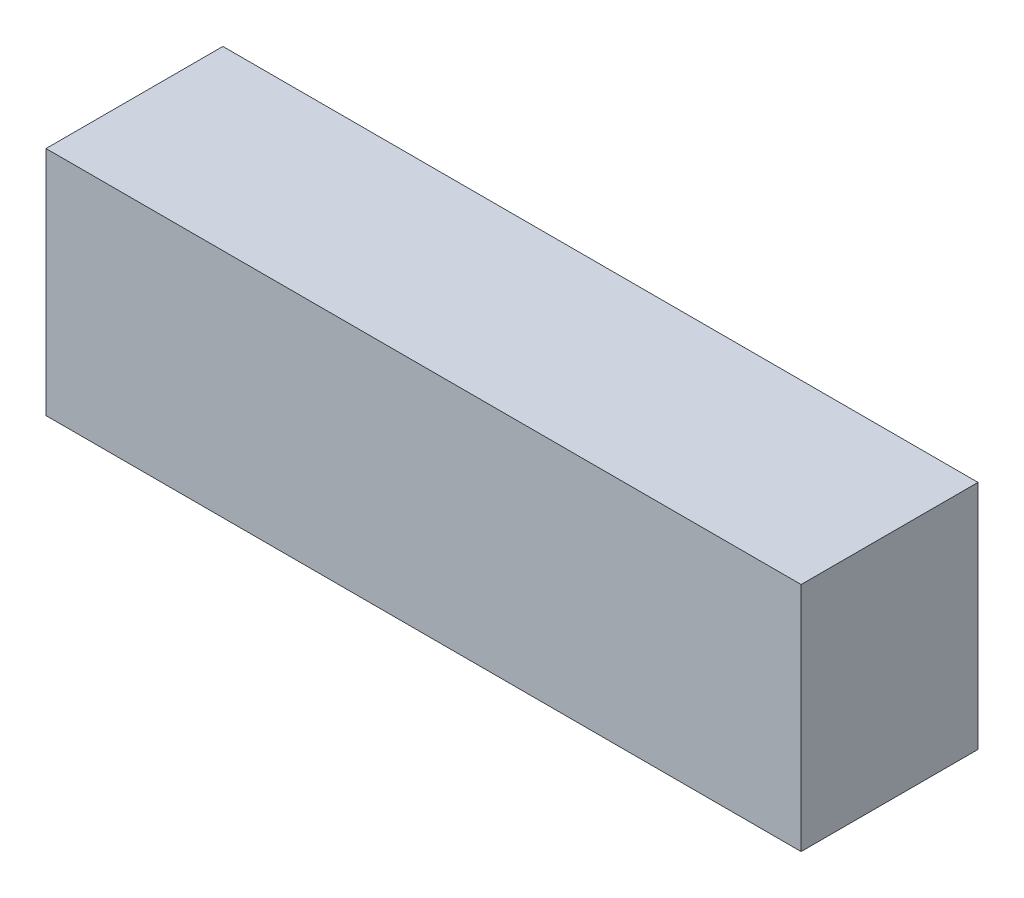
SolidWorks part; units mm, degrees
ref_plane "Alzado" through (0, 0, 0) normal (0, 0, 1) x (1, 0, 0)
ref_plane "Planta" through (0, 0, 0) normal (0, 1, 0) x (1, 0, 0)
ref_plane "Vista lateral" through (0, 0, 0) normal (1, 0, 0) x (0, 0, -1)
sketch "Croquis1" plane through (0, 0, 0) normal (0, 0, 1) x (1, 0, 0)
  line L1 (0, 0) -> (111, 0)
  line L2 (0, 0) -> (0, 34)
  line L3 (0, 34) -> (111, 34)
  line L4 (111, 0) -> (111, 34)
  dimension "D1" = 111
  dimension "D2" = 34
extrude "Saliente-Extruir1" add sketch "Croquis1" along normal blind 26
